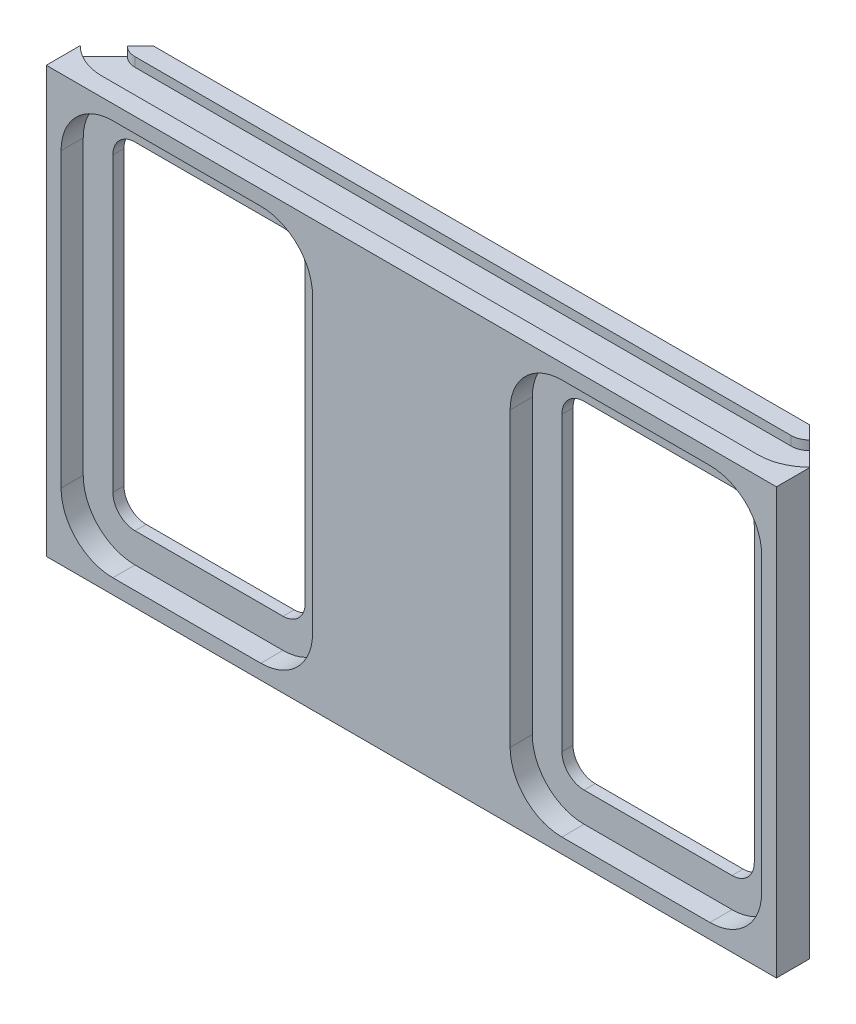
SolidWorks part; units mm, degrees
ref_plane "Front Plane" through (0, 0, 0) normal (0, 0, 1) x (1, 0, 0)
ref_plane "Top Plane" through (0, 0, 0) normal (0, 1, 0) x (1, 0, 0)
ref_plane "Right Plane" through (0, 0, 0) normal (1, 0, 0) x (0, 0, -1)
sketch "Sketch1" plane through (0, 0, 0) normal (0, 0, 1) x (1, 0, 0)
  line L2 (-98.7, -38.015) -> (-98.7, 76.985)
  line L5 (-98.7, 76.985) -> (98.7, 76.985)
  line L9 (98.7, 76.985) -> (98.7, -38.015)
  line L14 (98.7, -38.015) -> (-98.7, -38.015)
  dimension "D1" = 115
extrude "Boss-Extrude1" add sketch "Sketch1" along normal blind 9
sketch "Sketch2" plane through (0, 76.985, 0) normal (0, 1, 0) x (1, 0, 0)
  line L0 (-88.7, 10) -> (88.7, 10)
  line L1 (98.7, 0) -> (-98.7, 0) construction
  line L2 (-98.7, 0) -> (-88.7, 10)
  line L3 (98.7, 0) -> (88.7, 10)
  line L5 (-98.7, 0) -> (98.7, 0)
  dimension "D1" = 10
extrude "Boss-Extrude2" add sketch "Sketch2" against normal blind 10
sketch "Sketch3" plane through (0, 0, 9) normal (0, 0, 1) x (1, 0, 0)
  line L0 (-98.7, -38.015) -> (98.7, -38.015) construction
  line L1 (-80.7, 64.985) -> (-40.7, 64.985)
  line L2 (-86.7, 58.985) -> (-86.7, -20.015)
  line L3 (-80.7, -26.015) -> (-40.7, -26.015)
  line L4 (-34.7, 58.985) -> (-34.7, -20.015)
  line L6 (98.7, 76.985) -> (-98.7, 76.985) construction
  line L7 (-98.7, 76.985) -> (-98.7, -38.015) construction
  line L8 (-26.7, 19.985) -> (-26.7, 32.685) construction
  arc A0 (-86.7, -20.015) -> (-80.7, -26.015) centre (-80.7, -20.015) ccw
  arc A1 (-40.7, -26.015) -> (-34.7, -20.015) centre (-40.7, -20.015) ccw
  arc A2 (-40.7, 64.985) -> (-34.7, 58.985) centre (-40.7, 58.985) cw
  arc A3 (-80.7, 64.985) -> (-86.7, 58.985) centre (-80.7, 58.985) ccw
  dimension "D2" = 6
  dimension "D1" = 12
  dimension "D3" = 12
  dimension "D4" = 12
  dimension "D5" = 8
extrude "Cut-Extrude1" cut sketch "Sketch3" against normal up to surface (9 mm away) up to face at (0, 14.485, 0)
sketch "Sketch4" plane through (0, 0, 9) normal (0, 0, 1) x (1, 0, 0)
  line L8 (-94.7, 58.985) -> (-94.7, -20.015)
  line L9 (-80.7, -34.015) -> (-40.7, -34.015)
  line L10 (-26.7, -20.015) -> (-26.7, 58.985)
  line L11 (-40.7, 72.985) -> (-80.7, 72.985)
  line L12 (-94.7, 58.985) -> (-94.7, -20.015)
  line L13 (-80.7, -34.015) -> (-40.7, -34.015)
  line L14 (-26.7, -20.015) -> (-26.7, 58.985)
  line L15 (-40.7, 72.985) -> (-80.7, 72.985)
  arc A8 (-94.7, -20.015) -> (-80.7, -34.015) centre (-80.7, -20.015) ccw
  arc A9 (-40.7, -34.015) -> (-26.7, -20.015) centre (-40.7, -20.015) ccw
  arc A10 (-26.7, 58.985) -> (-40.7, 72.985) centre (-40.7, 58.985) ccw
  arc A11 (-80.7, 72.985) -> (-94.7, 58.985) centre (-80.7, 58.985) ccw
  arc A12 (-94.7, -20.015) -> (-80.7, -34.015) centre (-80.7, -20.015) ccw
  arc A13 (-40.7, -34.015) -> (-26.7, -20.015) centre (-40.7, -20.015) ccw
  arc A14 (-26.7, 58.985) -> (-40.7, 72.985) centre (-40.7, 58.985) ccw
  arc A15 (-80.7, 72.985) -> (-94.7, 58.985) centre (-80.7, 58.985) ccw
  dimension "D1" = 8
extrude "Cut-Extrude2" cut sketch "Sketch4" against normal blind 6
mirror "Mirror1" about plane through (0, 0, 0) normal (1, 0, 0) of "Cut-Extrude2", "Cut-Extrude1"
sketch "Sketch5" plane through (0, 76.985, 0) normal (0, 1, 0) x (1, 0, 0)
  line L0 (-88.7, 5) -> (88.7, 5)
  line L1 (-88.7, 10) -> (-98.7, 0) construction
  line L2 (98.7, 0) -> (88.7, 10) construction
  line L3 (88.7, 10) -> (-88.7, 10) construction
  line L4 (-88.7, -4) -> (88.7, -4)
  line L11 (-98.5995, 0.1005) -> (-92.2355, 6.4645)
  line L12 (92.2355, 6.4645) -> (98.5995, 0.1005)
  arc A0 (-88.7, 5) -> (-92.2355, 6.4645) centre (-88.7, 10) cw
  arc A1 (88.7, 5) -> (92.2355, 6.4645) centre (88.7, 10) ccw
  arc A2 (88.7, -4) -> (98.5995, 0.1005) centre (88.7, 10) ccw
  arc A3 (-88.7, -4) -> (-98.5995, 0.1005) centre (-88.7, 10) cw
  dimension "D1" = 5
  dimension "D2" = 9
extrude "Cut-Extrude3" cut sketch "Sketch5" against normal blind 2.5
